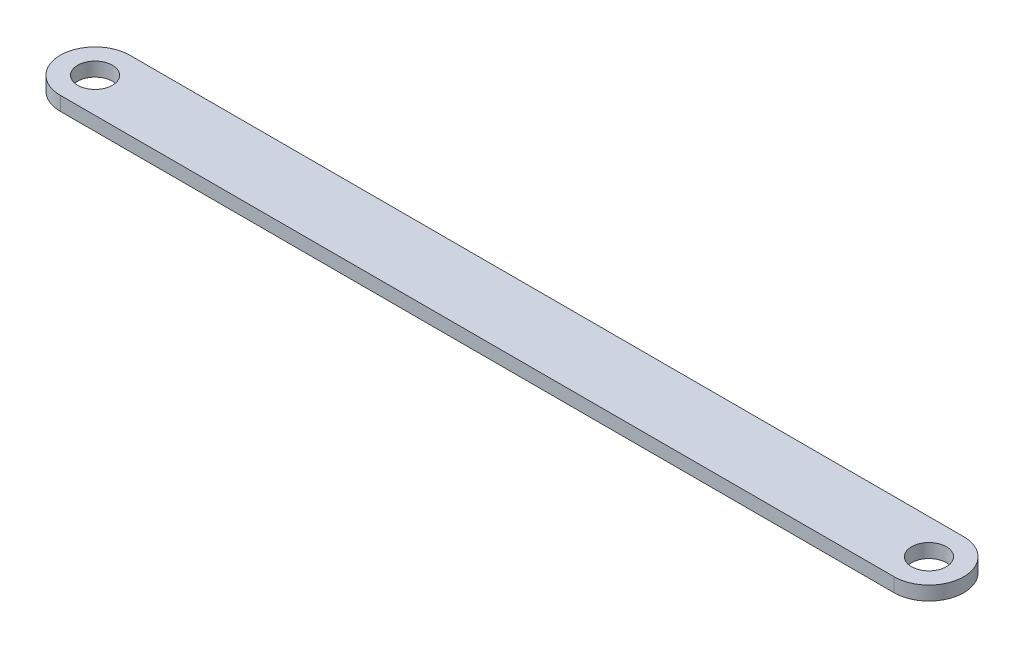
SolidWorks part; units mm, degrees
material "AISI 1020"
ref_plane "Front Plane" through (0, 0, 0) normal (0, 0, 1) x (1, 0, 0)
ref_plane "Top Plane" through (0, 0, 0) normal (0, 1, 0) x (1, 0, 0)
ref_plane "Right Plane" through (0, 0, 0) normal (1, 0, 0) x (0, 0, -1)
sketch "Sketch2" plane through (0, 0, 0) normal (0, 1, 0) x (1, 0, 0)
  line L0 (-76.2, 0) -> (76.2, 0) construction
  line L1 (0, 0) -> (0, 27.8548) construction
  line L2 (-76.2, 6.35) -> (76.2, 6.35)
  line L3 (76.2, -6.35) -> (-76.2, -6.35)
  arc A0 (-76.2, 6.35) -> (-76.2, -6.35) centre (-76.2, 0) ccw
  arc A1 (76.2, 6.35) -> (76.2, -6.35) centre (76.2, 0) cw
  circle A2 centre (76.2, 0) radius 3.175
  circle A3 centre (-76.2, 0) radius 3.175
  point P3 (0, 0)
  dimension "D2" = 12.7
  dimension "D3" = 6.35
  dimension "D1" = 152.4
extrude "Boss-Extrude1" add sketch "Sketch2" along normal mid plane 2.54
